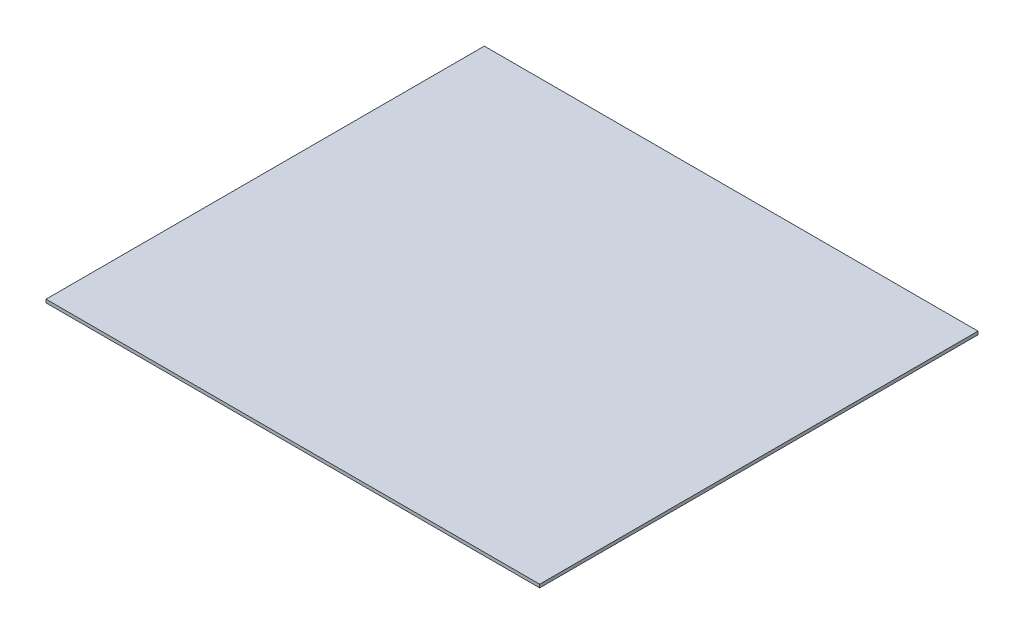
SolidWorks part; units mm, degrees
ref_plane "Спереди" through (0, 0, 0) normal (0, 0, 1) x (1, 0, 0)
ref_plane "Сверху" through (0, 0, 0) normal (0, 1, 0) x (1, 0, 0)
ref_plane "Справа" through (0, 0, 0) normal (1, 0, 0) x (0, 0, -1)
sketch "Эскиз1" plane through (0, 0, 0) normal (0, 0, 1) x (1, 0, 0)
  line L0 (-230.8846, 3) -> (230.8846, 3)
  line L1 (230.8846, 3) -> (230.8846, 0)
  line L2 (230.8846, 0) -> (-230.8846, 0)
  line L3 (-230.8846, 0) -> (-230.8846, 3)
extrude "Бобышка-Вытянуть1" add sketch "Эскиз1" against normal blind 410
